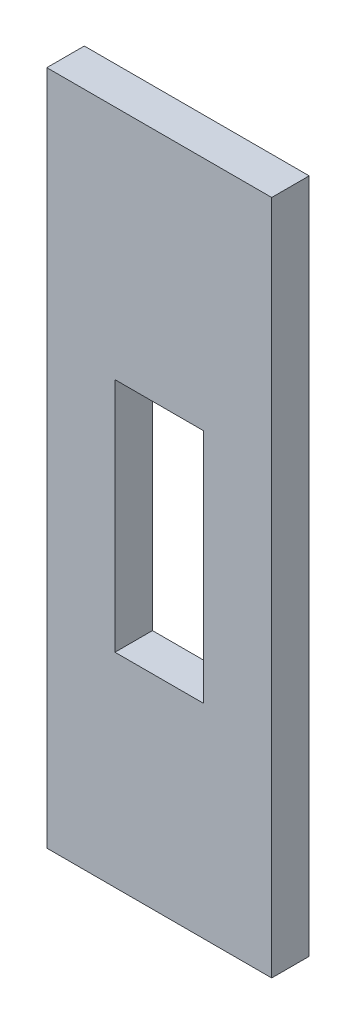
SolidWorks part; units mm, degrees
ref_plane "Front Plane" through (0, 0, 0) normal (0, 0, 1) x (1, 0, 0)
ref_plane "Top Plane" through (0, 0, 0) normal (0, 1, 0) x (1, 0, 0)
ref_plane "Right Plane" through (0, 0, 0) normal (1, 0, 0) x (0, 0, -1)
sketch "Sketch1" plane through (0, 0, 0) normal (0, 0, 1) x (1, 0, 0)
  line L0 (6.35, -129.3706) -> (0, -129.3706) construction
  line L1 (6.35, -243.8934) -> (-31.75, -243.8934)
  line L2 (6.35, -243.8934) -> (6.35, -129.3706)
  line L3 (6.35, -129.3706) -> (-31.75, -129.3706)
  line L4 (-31.75, -243.8934) -> (-31.75, -129.3706)
  line L5 (6.35, -129.3706) -> (6.35, -243.8934) construction
  line L8 (-20.2, -169.3706) -> (-5.2, -169.3706)
  line L9 (-20.2, -169.3706) -> (-20.2, -209.3706)
  line L10 (-20.2, -209.3706) -> (-5.2, -209.3706)
  line L11 (-5.2, -169.3706) -> (-5.2, -209.3706)
  dimension "D1" = 11.55
  dimension "D2" = 15
  dimension "D3" = 40
  dimension "D4" = 40
extrude "Boss-Extrude1" add sketch "Sketch1" along normal blind 6.35
